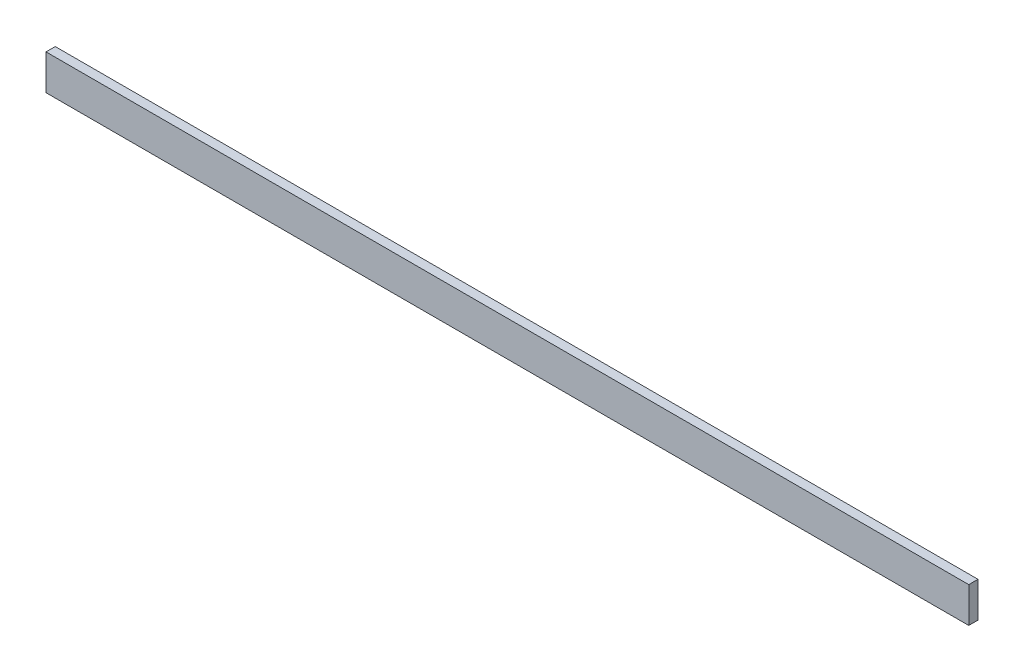
SolidWorks part; units mm, degrees
ref_plane "Front Plane" through (0, 0, 0) normal (0, 0, 1) x (1, 0, 0)
ref_plane "Top Plane" through (0, 0, 0) normal (0, 1, 0) x (1, 0, 0)
ref_plane "Right Plane" through (0, 0, 0) normal (1, 0, 0) x (0, 0, -1)
sketch "Sketch1" plane through (0, 0, 0) normal (0, 0, 1) x (1, 0, 0)
  line L0 (0, 0) -> (998.7571, 0)
  line L1 (998.7571, 0) -> (998.7571, 38.2926)
  line L2 (998.7571, 38.2926) -> (0, 38.2926)
  line L3 (0, 38.2926) -> (0, 0)
extrude "Boss-Extrude1" add sketch "Sketch1" along normal blind 10
